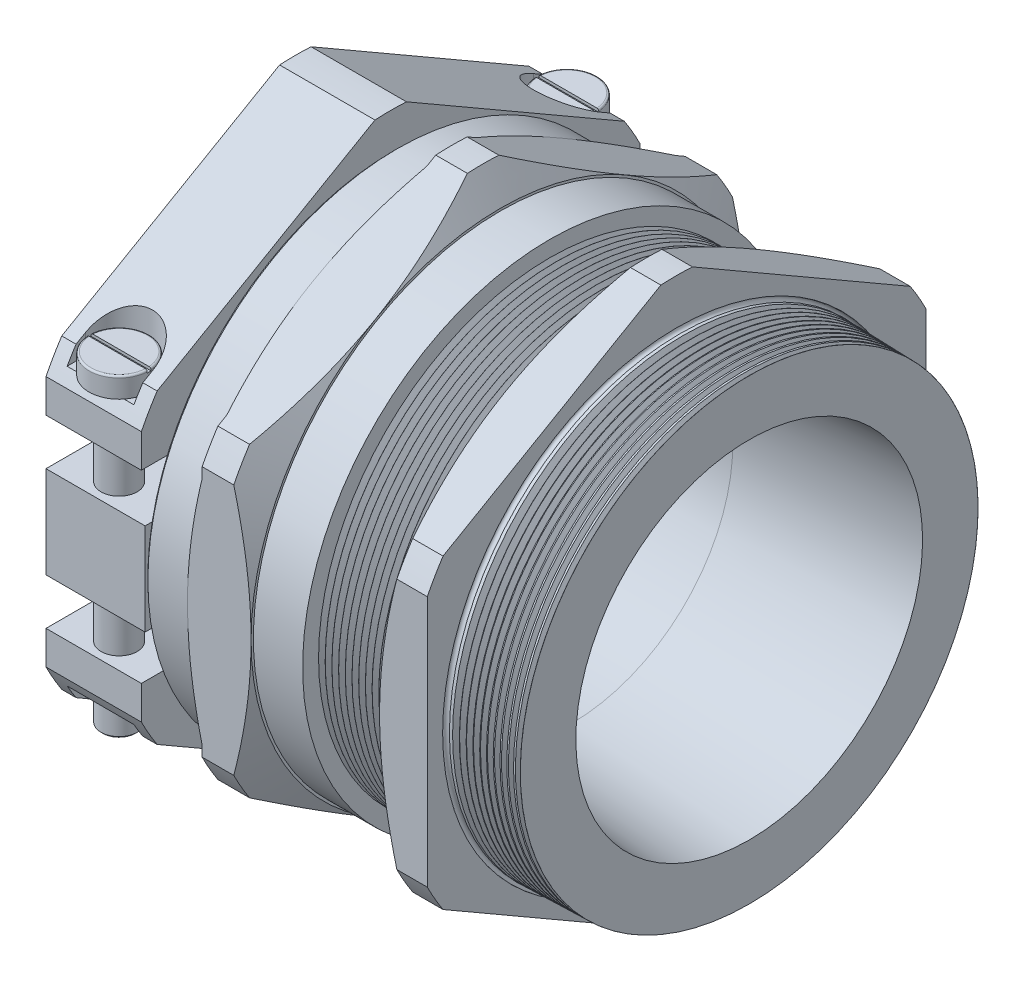
SolidWorks part; units mm, degrees
ref_plane "Front Plane" through (0, 0, 0) normal (0, 0, 1) x (1, 0, 0)
ref_plane "Top Plane" through (0, 0, 0) normal (0, 1, 0) x (1, 0, 0)
ref_plane "Right Plane" through (0, 0, 0) normal (1, 0, 0) x (0, 0, -1)
ref_plane "Plane1" through (0, -18.8976, 0) normal (0, 1, 0) x (-1, 0, 0)
sketch "Sketch1" plane through (0, 0, 0) normal (0, 0, 1) x (1, 0, 0)
  line L0 (-81.4901, 0) -> (81.4901, 0) construction
  line L1 (24.2126, 23.6641) -> (24.2126, 31.2373)
  line L2 (24.2126, 31.2373) -> (14.3319, 31.496)
  line L3 (14.3319, 31.496) -> (14.3319, 31.5468)
  line L4 (14.3319, 31.5468) -> (14.3066, 31.5468)
  line L5 (14.3066, 31.5468) -> (14.3066, 38.1203)
  line L6 (14.3066, 38.1203) -> (7.7978, 38.1203)
  line L7 (7.7978, 38.1203) -> (7.7978, 31.5468)
  line L8 (0, 21.971) -> (24.2126, 23.6641)
  line L9 (-24.2125, 28.5623) -> (-18.427, 28.5623)
  line L10 (7.7978, 31.5468) -> (-3.0247, 31.5468)
  line L11 (-9.7487, 33.7185) -> (-9.7487, 38.1203)
  line L12 (-9.7487, 38.1203) -> (-18.427, 38.1203)
  line L13 (-18.427, 38.1203) -> (-18.427, 34.036)
  line L14 (-18.427, 34.036) -> (-24.2125, 34.036)
  line L15 (-24.2125, 34.036) -> (-24.2125, 28.5623)
  line L16 (-18.427, 21.971) -> (0, 21.971)
  line L17 (0, 47.389) -> (0, -18.7473) construction
  line L18 (-24.7205, 21.971) -> (-37.738, 21.971)
  line L19 (-24.7205, 21.971) -> (-24.7205, 38.1203)
  line L20 (-24.7205, 38.1203) -> (-37.738, 38.1203)
  line L21 (-37.738, 21.971) -> (-37.738, 38.1203)
  line L22 (-18.427, 28.5623) -> (-18.427, 21.971)
  line L23 (-3.0247, 33.7185) -> (-9.7487, 33.7185)
  line L24 (-3.0247, 33.7185) -> (-3.0247, 31.5468)
  dimension "D1" = 4
  dimension "Cable dia" = 43.942
  dimension "D2" = 0.0254
  dimension "E/E1+" = 76.2406
  dimension "D3" = 57.1246
  dimension "D4" = 68.072
  dimension "Th+" = 63.0936
  dimension "D5" = 0.508
  dimension "1.5NW" = 13.0175
  dimension "NW1" = 8.6783
  dimension "NW3" = 6.5087
  dimension "B" = 52.07
  dimension "D" = 9.906
  dimension "D6" = 5.7856
  dimension "D7" = 6.7239
  dimension "Th" = 62.992
  dimension "angle" = 1.5
  dimension "D8" = 0.3175
revolve "Revolve1" add sketch "Sketch1" angle 360 about L0
sketch "Sketch2" plane through (14.3066, 0, 0) normal (1, 0, 0) x (0, 0, -1)
  line L1 (-2.1509, 38.0596) -> (-31.8851, 20.8925)
  line L2 (-34.036, 17.1671) -> (-34.036, -17.1671)
  line L3 (-31.8851, -20.8925) -> (-2.1509, -38.0596)
  line L4 (2.1509, -38.0596) -> (31.8851, -20.8925)
  line L5 (34.036, -17.1671) -> (34.036, 17.1671)
  line L6 (31.8851, 20.8925) -> (2.1509, 38.0596)
  circle A0 centre (0, 0) radius 34.036 construction
  circle A1 centre (0, 0) radius 38.1203 construction
  arc A2 (31.8851, -20.8925) -> (34.036, -17.1671) centre (0, 0) ccw
  arc A3 (-2.1509, -38.0596) -> (2.1509, -38.0596) centre (0, 0) ccw
  arc A4 (-34.036, -17.1671) -> (-31.8851, -20.8925) centre (0, 0) ccw
  arc A5 (-31.8851, 20.8925) -> (-34.036, 17.1671) centre (0, 0) ccw
  arc A6 (2.1509, 38.0596) -> (-2.1509, 38.0596) centre (0, 0) ccw
  arc A7 (34.036, 17.1671) -> (31.8851, 20.8925) centre (0, 0) ccw
  dimension "E/E1" = 68.072
extrude "Cut-Extrude1" cut sketch "Sketch2" against normal up to surface (52.0446 mm away) flip side to cut up to face at (-37.738, -21.971, 0)
sketch "Sketch13" plane through (7.7978, 0, 0) normal (1, 0, 0) x (0, 0, -1)
  line L0 (-2.1509, 38.0596) -> (-31.8851, 20.8925) construction
  circle A0 centre (0, 0) radius 34.036
extrude "Cut1" cut sketch "Sketch13" along normal through all draft 60 flip side to cut
sketch "Sketch14" plane through (-9.7487, 0, 0) normal (1, 0, 0) x (0, 0, -1)
  line L0 (-34.036, -17.1671) -> (-34.036, 17.1671) construction
  circle A0 centre (0, 0) radius 34.036
extrude "Cut2" cut sketch "Sketch14" against normal through all draft 60 flip side to cut
sketch "Sketch15" plane through (-18.427, 0, 0) normal (-1, 0, 0) x (0, 0, 1)
  line L0 (34.036, 17.1671) -> (34.036, 0) construction
  circle A0 centre (0, 0) radius 34.036
extrude "Cut3" cut sketch "Sketch15" against normal blind 2 draft 60 flip side to cut
chamfer "Chamfer1" distance 0.381 angle 45 1 edges at (-24.2126, -34.036, 0)
sketch "Sketch3" plane through (-37.738, 0, 0) normal (-1, 0, 0) x (0, 0, 1)
  line L0 (-34.036, 17.1671) -> (-34.036, -17.1671) construction
  line L1 (-34.036, 12.5984) -> (34.036, 12.5984)
  line L2 (-34.036, 12.5984) -> (-34.036, -12.5984)
  line L3 (-34.036, -12.5984) -> (34.036, -12.5984)
  line L4 (34.036, 12.5984) -> (34.036, -12.5984)
  line L5 (34.036, -17.1671) -> (34.036, 17.1671) construction
  line L6 (-54.4764, 0) -> (63.1151, 0) construction
  dimension "D1" = 25.1968
extrude "Cut-Extrude2" cut sketch "Sketch3" against normal up to surface (13.0175 mm away) up to face at (-24.7205, -21.971, 0)
sketch "Sketch4" plane through (-24.2125, 0, 0) normal (-1, 0, 0) x (0, 0, 1)
  line L0 (85.5301, 0) -> (-85.5301, 0) construction
  line L1 (34.036, 6.2774) -> (21.0551, 6.2774)
  line L2 (34.036, 6.2774) -> (34.036, -6.2774)
  line L3 (34.036, -6.2774) -> (21.0551, -6.2774)
  line L4 (34.036, -15.7419) -> (34.036, 0) construction
  line L6 (0, 92.5502) -> (0, -95.2315) construction
  line L8 (-34.036, -6.2774) -> (-21.0551, -6.2774)
  line L9 (-34.036, 6.2774) -> (-34.036, -6.2774)
  line L10 (-34.036, 6.2774) -> (-21.0551, 6.2774)
  arc A2 (21.0551, 6.2774) -> (21.0551, -6.2774) centre (0, 0) cw
  arc A5 (-21.0551, 6.2774) -> (-21.0551, -6.2774) centre (0, 0) ccw
  circle A8 centre (0, 0) radius 21.971 construction
  dimension "D1" = 12.5549
extrude "Extrude1" add sketch "Sketch4" along normal up to vertex (13.5255 mm away) up to point (-37.738, 21.971, 0)
sketch "Sketch5" plane through (0, -18.8976, 0) normal (0, 1, 0) x (1, 0, 0)
  line L0 (-25.4892, 0) -> (25.3265, 0) construction
  line L1 (-37.738, -34.036) -> (-24.7205, -34.036) construction
  line L3 (-35.7854, -30.5647) -> (-35.7854, -34.036)
  line L4 (-35.7854, -34.036) -> (-26.6732, -34.036)
  line L5 (-26.6732, -30.5647) -> (-26.6732, -34.036)
  line L6 (-37.738, -31.8851) -> (-37.738, -2.1509) construction
  line L7 (-31.2293, 8.138) -> (-31.2293, -18.0549) construction
  line L8 (-24.7205, -31.8851) -> (-24.7205, -2.1509) construction
  arc A0 (-35.7854, -30.5647) -> (-26.6732, -30.5647) centre (-31.2293, -30.5647) cw
  dimension "D2" = 3.4713
  dimension "D1" = 9.1122
extrude "Cut-Extrude3" cut sketch "Sketch5" against normal through all
mirror "Mirror1" about plane through (0, 0, 0) normal (0, 1, 0) of "Cut-Extrude3"
mirror "Mirror2" about plane through (0, 0, 0) normal (0, 0, 1) of "Mirror1", "Cut-Extrude3"
sketch "Sketch6" plane through (0, 18.8976, 0) normal (0, -1, 0) x (1, 0, 0)
  circle A0 centre (-31.2293, 30.5647) radius 4.1005
  arc A1 (-35.7854, 30.5647) -> (-26.6732, 30.5647) centre (-31.2293, 30.5647) ccw construction
  dimension "D1" = 8.201
extrude "Extrude2" add sketch "Sketch6" against normal up to vertex (2.7573 mm away)
sketch "Sketch7" plane through (0, 12.5984, 0) normal (0, 1, 0) x (-1, 0, 0)
  circle A1 centre (31.2293, 30.5647) radius 4.1005 construction
  circle A2 centre (31.2293, 30.5647) radius 2.4603
  circle A3 centre (31.2293, 30.5647) radius 4.1005 construction
  dimension "D1" = 4.9206
extrude "Extrude3" add sketch "Sketch7" against normal blind 34.9956
sketch "Sketch8" plane through (0, 21.6549, 0) normal (0, 1, 0) x (-1, 0, 0)
  line L0 (14.7933, 30.5647) -> (47.6653, 30.5647) construction
  line L1 (27.1367, 30.8187) -> (35.3219, 30.8187)
  line L3 (27.1367, 30.3107) -> (35.3219, 30.3107)
  arc A1 (35.3219, 30.3107) -> (35.3219, 30.8187) centre (31.2293, 30.5647) ccw
  circle A3 centre (31.2293, 30.5647) radius 4.1005 construction
  arc A4 (27.1367, 30.8187) -> (27.1367, 30.3107) centre (31.2293, 30.5647) ccw
  dimension "D1" = 0.508
extrude "Cut-Extrude4" cut sketch "Sketch8" against normal blind 0.381
fillet "Fillet1" radius 0.254 2 edges at (-31.2293, 21.6549, 26.4642) (-31.2293, 21.6549, 34.6652)
mirror "Mirror3" about plane through (0, 0, 0) normal (0, 0, 1) of "Extrude2", "Fillet1", "Cut-Extrude4", "Extrude3"
sketch "Sketch11" plane through (0, 0, 0) normal (0, 0, 1) x (1, 0, 0)
  line L0 (-3.0247, 31.5468) -> (-2.1219, 31.5468)
  line L1 (7.7978, 31.5468) -> (-3.0247, 31.5468) construction
  line L2 (-2.1219, 31.5468) -> (-2.5733, 30.765)
  line L3 (-2.5733, 30.765) -> (-3.0247, 31.5468)
  line L4 (-3.0247, -31.5468) -> (-3.0247, 31.5468) construction
  line L5 (-25.4189, 0) -> (25.4189, 0) construction
  line L8 (-2.5733, 31.5468) -> (-2.5733, 30.765) construction
  dimension "D2" = 60
  dimension "H" = 0.7818
revolve "Cut-Revolve1" cut sketch "Sketch11" angle 360 about L5
pattern_linear "LPattern1" count 12 spacing 0.9144 along (1, 0, 0) of "Cut-Revolve1"
sketch "Sketch12" plane through (0, 0, 0) normal (0, 0, 1) x (1, 0, 0)
  line L0 (15.1956, 31.4734) -> (16.0989, 31.4497)
  line L2 (16.0989, 31.4497) -> (15.654, 30.6793)
  line L3 (15.654, 30.6793) -> (15.1956, 31.4734)
  line L6 (14.3066, 38.0596) -> (14.3066, 20.8925) construction
  line L7 (24.2126, 31.2373) -> (14.3319, 31.496) construction
  dimension "D1" = 30
  dimension "D2" = 60
  dimension "D3" = 0.7818
  dimension "D4" = 0.889
revolve "Cut-Revolve2" cut sketch "Sketch12" angle 360 about axis through (-81.4901, 0, 0) along (1, 0, 0)
pattern_linear "LPattern2" count 10 spacing 0.9144 along (1, 0, 0) of "Cut-Revolve2"
sketch "Sketch16" plane through (0, 0, 0) normal (0, 0, 1) x (1, 0, 0)
  line L0 (14.3319, -31.5468) -> (14.3319, 31.5468) construction
  line L1 (14.3319, -31.496) -> (15.1956, -31.4734) construction
  line L2 (-3.3815, 0) -> (18.0455, 0) construction
  circle A0 centre (14.3319, -31.496) radius 0.4445
  dimension "D1" = 0.889
sketch "Sketch17" plane through (0, 0, 0) normal (0, 0, 1) x (1, 0, 0)
  line L0 (0, 21.971) -> (-18.427, 21.971) construction
  line L1 (-18.427, 0) -> (-18.427, 29.476) construction
  line L2 (-23.4505, 28.5623) -> (-18.427, 28.5623)
  line L3 (-23.4505, 28.5623) -> (-23.4505, 21.971)
  line L4 (-23.4505, 21.971) -> (-18.427, 21.971)
  line L7 (13.86, 0) -> (-29.9484, 0) construction
  line L8 (-18.427, 28.5623) -> (-18.427, 21.971)
  line L11 (-24.2125, 33.655) -> (-24.2125, -33.655) construction
  line L12 (-18.427, 28.5623) -> (-24.2125, 28.5623) construction
  dimension "D1" = 0.762
revolve "Revolve3" add sketch "Sketch17" angle 360 about L7
sketch "Sketch18" [suppressed] plane through (0, 0, 0) normal (0, 0, 1) x (1, 0, 0)
  line L0 (-18.427, 22.7838) -> (-22.9426, 22.7838)
  line L1 (-18.427, 22.7838) -> (-24.2126, 22.7838) construction
  line L2 (-23.1966, 22.5298) -> (-23.1965, 17.526)
  line L3 (-23.1965, 17.526) -> (-18.427, 17.526)
  line L4 (-18.427, 17.526) -> (-18.427, 22.7838)
  line L5 (-18.427, 22.7838) -> (-18.427, -22.7838) construction
  line L7 (0, 17.526) -> (-18.427, 17.526) construction
  line L8 (-24.2126, 33.655) -> (-24.2126, 5.0074) construction
  line L9 (13.704, 0) -> (-22.4857, 0) construction
  arc A0 (-22.9426, 22.7838) -> (-23.1966, 22.5298) centre (-22.9426, 22.5298) ccw
  dimension "D1" = 0.254
  dimension "D2" = 1.016
revolve "Revolve4" [suppressed] add sketch "Sketch18" angle 360 about L9
revolve "Cut-Revolve3" cut sketch "Sketch16" angle 360 about L2
chamfer "Chamfer2" distance 0.254 angle 45 2 edges at (-33.6896, -22.3972, 30.5647) (-33.6896, -22.3972, -30.5647)
equation "\"D3@Sketch1\" = \"Cable dia@Sketch1\"*1.3"
